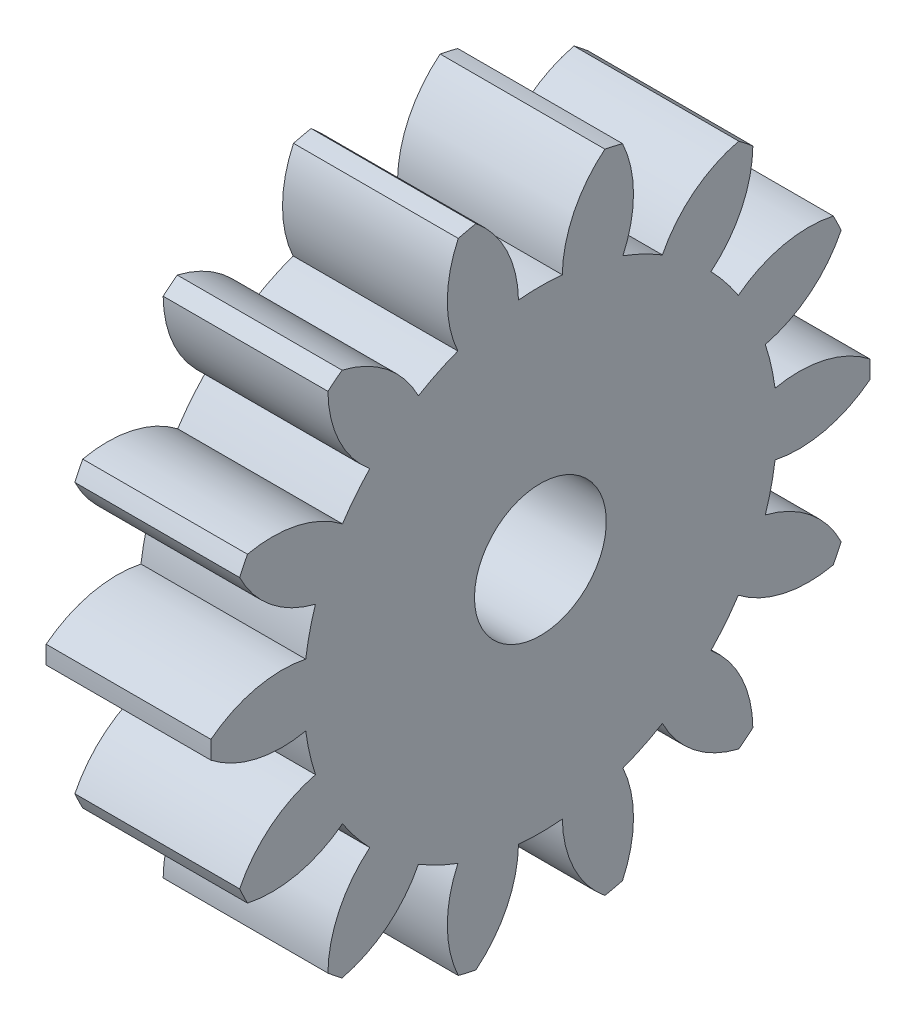
SolidWorks part; units mm, degrees
ref_plane "Plane1" through (0, 0, 0) normal (0, 0, 1) x (1, 0, 0)
ref_plane "Plane2" through (0, 0, 0) normal (0, 1, 0) x (1, 0, 0)
ref_plane "Plane3" through (0, 0, 0) normal (1, 0, 0) x (0, 0, -1)
sketch "HoldingSke" plane through (0, 0, 0) normal (0, 1, 0) x (1, 0, 0)
  line L0 (0, 0) -> (3.8812, -0.9677)
  line L1 (-15, 0) -> (100, 0) construction
  line L2 (0, 0) -> (-2.1039, 2.3779)
  line L3 (0, 0) -> (-11.863, 4.5341)
  line L4 (0, 0) -> (8.3795, 2.0892)
  line L5 (0, 0) -> (-46.8476, -17.4728)
  line L6 (0, 0) -> (-0.829, -0.5593)
  line L7 (-2.1039, 2.3779) -> (8.6586, 51.2059)
  line L8 (-76.2, 54.61) -> (-76.1, 54.61)
  line L9 (-71.009, 38.7566) -> (-53.1078, 45.2721)
  line L10 (-76.2, 71.12) -> (104.1128, 71.12)
  line L11 (0, 0) -> (-1, 0)
  line L12 (-76.2, 101.6) -> (-76.192, 101.6)
  line L13 (24.9733, 27.94) -> (52.9518, 28.4284)
  line L14 (24.9733, 27.94) -> (24.9743, 27.94)
  line L15 (24.9733, 27.94) -> (100.4006, 29.5858)
  line L16 (-63.627, -0.25) -> (-12.827, -0.25)
  circle A0 centre (0, 0) radius 0.4
  circle A1 centre (0, 0) radius 1.4365
  circle A2 centre (0, 0) radius 37.5
  circle A3 centre (0, 0) radius 0.4
  dimension "MHD" = 2.873
  dimension "Hub_dia" = 75
  dimension "Bore" = 0.8
  dimension "MBD" = 0.8
  dimension "Num_teeth" = 14
  dimension "Pitch" = 4
  dimension "Overall_len" = 50
  dimension "Show_teeth" = 14
  dimension "Thickness" = 1
  dimension "OAL" = 50.0001
  dimension "T_dim" = 0.1
  dimension "Ap" = 20
  dimension "H" = 19.05
  dimension "Pitch_radius" = 180.3128
  dimension "Width" = 1
  dimension "Backlash" = 0.008
  dimension "Addendum_fac" = 1
  dimension "Dedendum_fac" = 1.25
  dimension "Clearance_fac" = 0.25
  dimension "Dedendum_add" = 0.001
  dimension "Module" = 0.25
sketch "BasProSke" plane through (0, 0, 0) normal (0, 1, 0) x (1, 0, 0)
  line L0 (-10, 0) -> (60, 0) construction
  line L1 (0, 0) -> (0, 2)
  line L2 (0, 0) -> (1, 0)
  line L3 (1, 0) -> (1, 2)
  line L4 (1, 2) -> (0, 2)
  dimension "Thickness" = 1
  dimension "Diameter" = 4
revolve "Base-Revolve" add sketch "BasProSke" angle 360 about L0
sketch "TooCutSke" plane through (0, 0, 0) normal (1, 0, 0) x (0, 0, -1)
  line L1 (0, 0) -> (0, 107) construction
  line L2 (0, 0) -> (-0.2099, 1.7374) construction
  line L3 (0, 0) -> (-0.7746, 3.3938) construction
  line L4 (-0.2099, 1.7374) -> (-0.3873, 1.6969) construction
  arc A0 (0.1329, 1.4303) -> (-0.1329, 1.4303) centre (0, 0) ccw
  arc A1 (0.418, 1.9818) -> (-0.418, 1.9818) centre (0, 0) ccw
  circle A2 centre (0, 0) radius 1.75 construction
  circle A3 centre (0, 0) radius 1.6445 construction
  arc A4 (-0.1329, 1.4303) -> (-0.418, 1.9818) centre (-0.8328, 1.418) ccw
  arc A5 (0.418, 1.9818) -> (0.1329, 1.4303) centre (0.8328, 1.418) ccw
  dimension "Root_dia" = 2.873
  dimension "Overcut_dia" = 4.0508
  dimension "Pitch_dia" = 3.5
  dimension "Base_dia" = 3.2889
  dimension "Flank_rad" = 0.7
  dimension "Half_ang" = 12.857
  dimension "Half_CT" = 0.1819
extrude "ToothCut" cut sketch "TooCutSke" along normal through all
fillet "Breaks" [suppressed] radius 0.005
fillet "RootFillets" [suppressed] radius 0.0635
pattern_circular "TeethCuts" count 14 every 25.714 about axis through (-10, 0, 0) along (1, 0, 0) of "ToothCut", "RootFillets", "Breaks"
sketch "HubNeaOneSke" plane through (0, 0, 0) normal (-1, 0, 0) x (0, 0, 1)
  circle A0 centre (0, 0) radius 1.4365
  dimension "Diameter" = 2.873
extrude "HubNearOne" [suppressed] add sketch "HubNeaOneSke" along normal blind 49.0001
sketch "HubNeaBotSke" plane through (0, 0, 0) normal (-1, 0, 0) x (0, 0, 1)
  circle A0 centre (0, 0) radius 1.4365
  dimension "Diameter" = 2.873
extrude "HubNearBoth" [suppressed] add sketch "HubNeaBotSke" along normal blind 24.5
ref_plane "FarPln" through (1, 0, 0) normal (1, 0, 0) x (0, 0, -1)
sketch "HubFarSke" plane through (1, 0, 0) normal (1, 0, 0) x (0, 0, -1)
  circle A0 centre (0, 0) radius 1.4365
  dimension "Diameter" = 2.873
extrude "HubFar" [suppressed] add sketch "HubFarSke" along normal blind 24.5
sketch "BorSke" plane through (0, 0, 0) normal (1, 0, 0) x (0, 0, -1)
  circle A0 centre (0, 0) radius 0.4
  dimension "Diameter" = 0.8
extrude "Bore" cut sketch "BorSke" along normal mid plane 100.0001
sketch "KeySke" plane through (0, 0, 0) normal (1, 0, 0) x (0, 0, -1)
  line L0 (-0.05, 0) -> (-0.05, 0.5)
  line L1 (-0.05, 0.5) -> (0.05, 0.5)
  line L2 (0.05, 0.5) -> (0.05, 0)
  line L3 (0, 0) -> (0, 34) construction
  line L4 (-0.05, 0) -> (0.05, 0)
  dimension "Offset" = 0.5
extrude "Keyway" [suppressed] cut sketch "KeySke" along normal mid plane 100.0001
pattern_circular "Keyway2" [suppressed] count 2 every 90 about axis through (-10, 0, 0) along (1, 0, 0)
equation "' \"Module@HoldingSke\" = 6.35"
equation "' \"Num_teeth@HoldingSke\" = 12"
equation "' \"Ap@HoldingSke\" =  20"
equation "' \"Ap@HoldingSke\" = 20"
equation "' \"Width@HoldingSke\" = 0.5 * 25.4"
equation "' \"Hub_dia@HoldingSke\"= 1 * 25.4"
equation "' \"Hub_dia@HoldingSke\" = 1 * 25.4"
equation "' \"Overall_len@HoldingSke\" = 1.0 * 25.4"
equation "' \"Bore@HoldingSke\" = 0.75 * 25.4"
equation "' \"T_dim@HoldingSke\" = 0.1 * 25.4"
equation "' \"Width@KeySke\" = 0.25 * 25.4"
equation "' \"Show_teeth@HoldingSke\" = 13"
equation "' \"Backlash@HoldingSke\" = 0.009 * 25.4"
equation "' \"Addendum_fac@HoldingSke\" = 1.0"
equation "' \"Dedendum_fac@HoldingSke\" = 1.25"
equation "' \"Dedendum_add@HoldingSke\" = 0.00005 * 25.4"
equation "' \"Clearance_fac@HoldingSke\" = 0.25"
equation "\"Pitch@HoldingSke\" = 1 / \"Module@HoldingSke\""
equation "\"Overcut_dia@TooCutSke\" = (\"Num_teeth@HoldingSke\" + 2 * \"Addendum_fac@HoldingSke\") / \"Pitch@HoldingSke\" + 0.002 * 25.4"
equation "\"Pitch_dia@TooCutSke\" = \"Num_teeth@HoldingSke\" / \"Pitch@HoldingSke\""
equation "\"Base_dia@TooCutSke\" = \"Num_teeth@HoldingSke\" / \"Pitch@HoldingSke\" * cos((\"Ap@HoldingSke\"  * 3.14159265 / 180))"
equation "\"Root_dia@TooCutSke\" = (\"Num_teeth@HoldingSke\" + 2) / \"Pitch@HoldingSke\" - 2 * (\"Addendum_fac@HoldingSke\" + \"Dedendum_fac@HoldingSke\") / \"Pitch@HoldingSke\" - \"Dedendum_add@HoldingSke\" * 2"
equation "\"Half_ang@TooCutSke\" = 180 / \"Num_teeth@HoldingSke\""
equation "\"Half_CT@TooCutSke\" = \"Num_teeth@HoldingSke\" / \"Pitch@HoldingSke\" * sin((3.14159265 / 2 / \"Num_teeth@HoldingSke\")) / 2 - 7 * \"Backlash@HoldingSke\" / 4"
equation "\"Flank_rad@TooCutSke\" = \"Num_teeth@HoldingSke\" / \"Pitch@HoldingSke\" / 5"
equation "\"Radius@RootFillets\" = \"Clearance_fac@HoldingSke\" / \"Pitch@HoldingSke\" + \"Dedendum_add@HoldingSke\""
equation "\"Break_rad@Breaks\" = 0.02 / \"Pitch@HoldingSke\""
equation "\"Thickness@HoldingSke\" = \"Width@HoldingSke\""
equation "\"OAL@HoldingSke\" = \"Thickness@HoldingSke\""
equation "\"MHD@HoldingSke\" = (\"Num_teeth@HoldingSke\" + 2) / \"Pitch@HoldingSke\" - 2 * (\"Addendum_fac@HoldingSke\" + \"Dedendum_fac@HoldingSke\")  / \"Pitch@HoldingSke\" - \"Dedendum_add@HoldingSke\" * 2"
equation "\"MBD@HoldingSke\" = (\"Num_teeth@HoldingSke\" + 2) / \"Pitch@HoldingSke\" - 2 * (\"Addendum_fac@HoldingSke\" + \"Dedendum_fac@HoldingSke\")  / \"Pitch@HoldingSke\" - \"Dedendum_add@HoldingSke\" * 2 - 0.002 * 25.4"
equation "\"MHD@HoldingSke\" = ((sgn( \"MHD@HoldingSke\" - \"Hub_dia@HoldingSke\" )-1)*( \"MHD@HoldingSke\" - \"Hub_dia@HoldingSke\" ))/-2+ \"Hub_dia@HoldingSke\""
equation "\"MBD@HoldingSke\" = ((sgn( \"MBD@HoldingSke\" - \"Bore@HoldingSke\" )-1)*( \"MBD@HoldingSke\" - \"Bore@HoldingSke\" ))/-2+ \"Bore@HoldingSke\""
equation "\"OAL@HoldingSke\" = ((sgn( \"OAL@HoldingSke\" - \"Overall_len@HoldingSke\" )+1)*( \"OAL@HoldingSke\" - \"Overall_len@HoldingSke\" ))/2 + \"Overall_len@HoldingSke\" + 0.000002 * 25.4"
equation "\"Num_teeth@TeethCuts\" = int( \"Show_teeth@HoldingSke\" ) + 1"
equation "\"Num_teeth@TeethCuts\" = ((sgn( \"Num_teeth@TeethCuts\" - \"Num_teeth@HoldingSke\" )-1)*( \"Num_teeth@TeethCuts\" - \"Num_teeth@HoldingSke\" ))/-2+ \"Num_teeth@HoldingSke\""
equation "\"Num_teeth@TeethCuts\" = ((sgn( \"Num_teeth@TeethCuts\" - 2.0)+1)*( \"Num_teeth@TeethCuts\" - 2.0))/2 +2.0"
equation "\"Angle@TeethCuts\" = 360.0 / \"Num_teeth@HoldingSke\""
equation "\"Diameter@BasProSke\" = (\"Num_teeth@HoldingSke\" + 2 * \"Addendum_fac@HoldingSke\") / \"Pitch@HoldingSke\""
equation "\"Thickness@BasProSke\"  = \"Thickness@HoldingSke\""
equation "' \"Fillet_rad@BasProSke\" =  \"Thickness@HoldingSke\" * 0.05"
equation "' \"Fillet_rad@BasProSke\" = \"Thickness@HoldingSke\" * 0.05"
equation "\"MHD@HoldingSke\" = ((sgn( \"MHD@HoldingSke\" - \"Root_dia@TooCutSke\" )-1)*( \"MHD@HoldingSke\" - \"Root_dia@TooCutSke\" ))/-2+ \"Root_dia@TooCutSke\""
equation "\"Diameter@HubNeaOneSke\" = \"MHD@HoldingSke\""
equation "\"Length@HubNearOne\" = \"OAL@HoldingSke\" - \"Thickness@BasProSke\""
equation "\"Diameter@HubNeaBotSke\" = \"MHD@HoldingSke\""
equation "\"Length@HubNearBoth\" = ( \"OAL@HoldingSke\" - \"Thickness@BasProSke\" ) / 2.0"
equation "\"Thickness@FarPln\" = \"Thickness@BasProSke\""
equation "\"Diameter@HubFarSke\" = \"MHD@HoldingSke\""
equation "\"Length@HubFar\" = ( \"OAL@HoldingSke\" - \"Thickness@BasProSke\" ) / 2.0"
equation "\"Diameter@BorSke\" = \"MBD@HoldingSke\""
equation "\"D1@Bore\" = \"OAL@HoldingSke\" * 2.0"
equation "\"D1@Keyway\" = \"OAL@HoldingSke\" * 2.0"
equation "\"Offset@KeySke\" = \"T_dim@HoldingSke\" + \"MBD@HoldingSke\" / 2.0"
